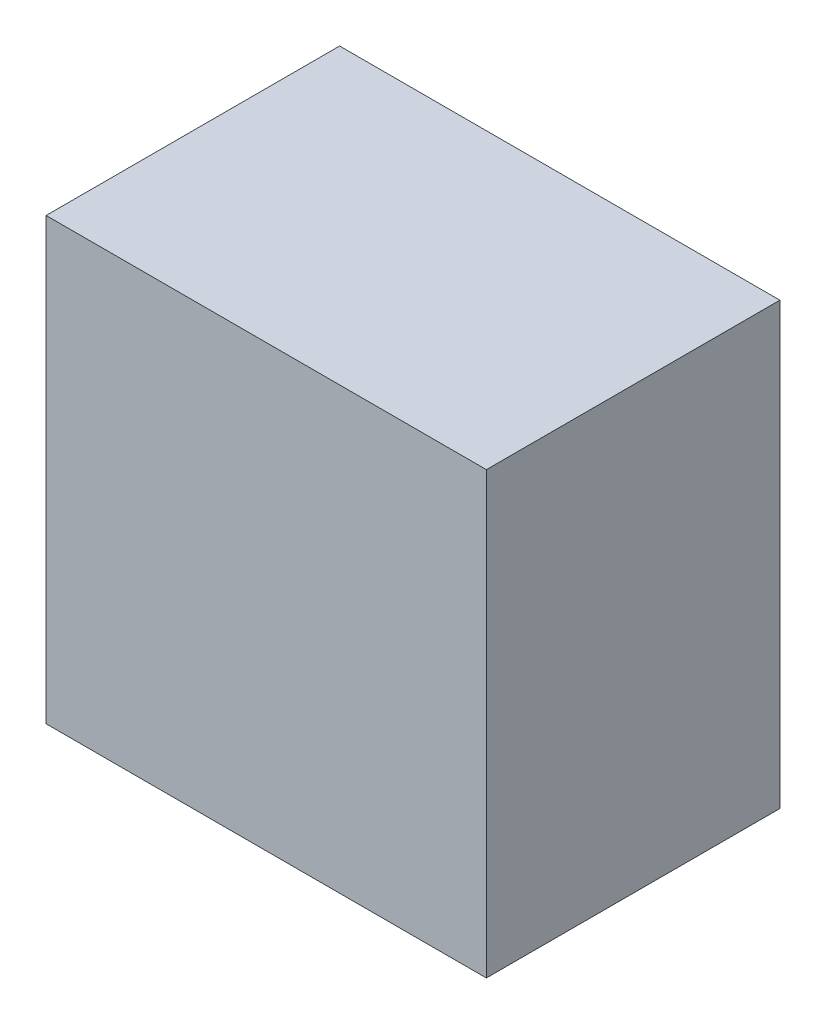
SolidWorks part; units mm, degrees
ref_plane "Front Plane" through (0, 0, 0) normal (0, 0, 1) x (1, 0, 0)
ref_plane "Top Plane" through (0, 0, 0) normal (0, 1, 0) x (1, 0, 0)
ref_plane "Right Plane" through (0, 0, 0) normal (1, 0, 0) x (0, 0, -1)
sketch "Sketch1" plane through (0, 0, 0) normal (0, 0, 1) x (1, 0, 0)
  line L1 (0, 0) -> (15, 0)
  line L2 (0, 0) -> (0, -15)
  line L3 (0, -15) -> (15, -15)
  line L4 (15, 0) -> (15, -15)
  dimension "D1" = 15
  dimension "D2" = 15
extrude "Boss-Extrude1" add sketch "Sketch1" along normal blind 10
ref_plane "Plane1" through (7.5, 0, 0) normal (1, 0, 0) x (0, 0, -1)
sketch "Sketch2" plane through (7.5, 0, 0) normal (1, 0, 0) x (0, 0, -1)
  line L1 (3, -10) -> (0, -10)
  line L2 (3, -10) -> (3, -5)
  line L3 (3, -5) -> (0, -5)
  line L4 (0, -10) -> (0, -5)
  line L5 (3, -10) -> (0, -5) construction
  line L6 (3, -5) -> (0, -10) construction
  line L7 (0, -15) -> (0, 0) construction
  line L8 (-10, -15) -> (0, -15) construction
  circle A0 centre (3, -7.5) radius 2.5
  circle A1 centre (3, -7.5) radius 1
  point P0 (1.5, -7.5)
  point P10 (0, -7.5)
  dimension "D4" = 2
  dimension "D1" = 5
  dimension "D2" = 5
  dimension "D3" = 3
extrude "Boss-Extrude2" add sketch "Sketch2" along normal mid plane 3 contours A1 L2 A0 | A1 L2 A0 | A0 L3 L4 L1
